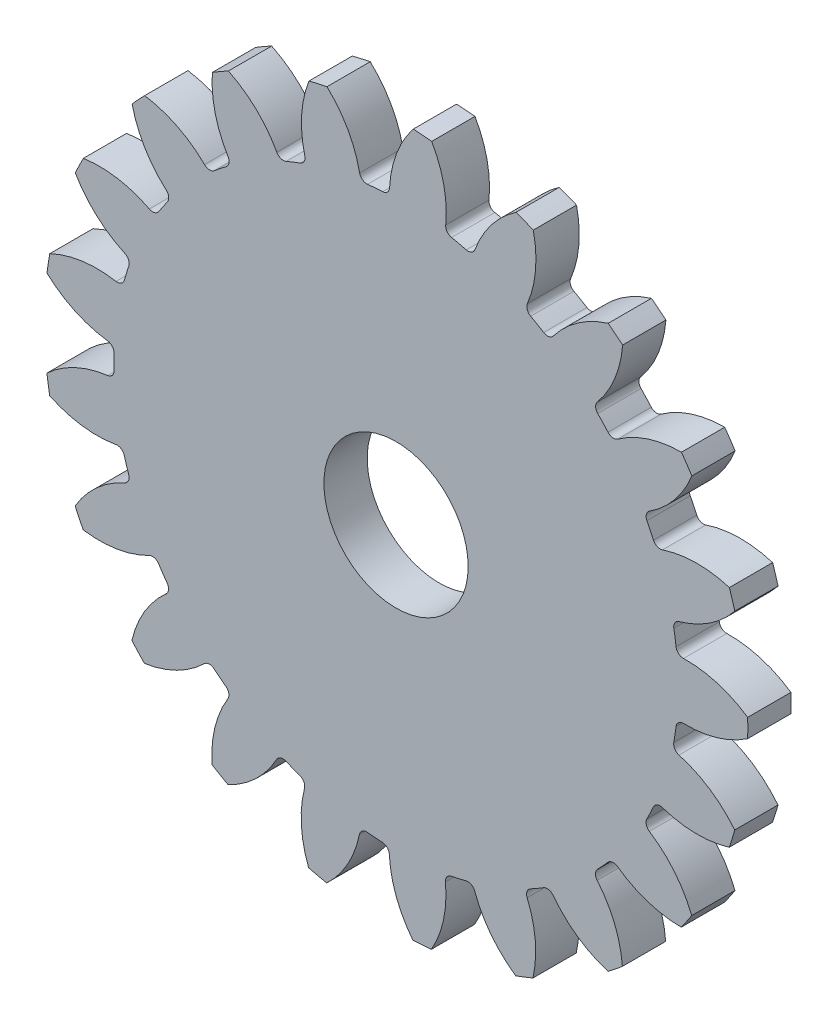
SolidWorks part; units mm, degrees
ref_plane "Alzado" through (0, 0, 0) normal (0, 0, 1) x (1, 0, 0)
ref_plane "Planta" through (0, 0, 0) normal (0, 1, 0) x (1, 0, 0)
ref_plane "Vista lateral" through (0, 0, 0) normal (1, 0, 0) x (0, 0, -1)
sketch "Croquis1" plane through (0, 0, 0) normal (0, 0, 1) x (1, 0, 0)
  circle A0 centre (0, 0) radius 24.384
  dimension "D1" = 48.768
extrude "Saliente-Extruir1" add sketch "Croquis1" along normal blind 3
sketch "Croquis2" plane through (0, 0, 3) normal (0, 0, 1) x (1, 0, 0)
  line L0 (0, 0) -> (0, 22.225) construction
  line L1 (0, 0) -> (8.7101, 23.9309) construction
  line L2 (0, 0) -> (-1.651, 22.1636) construction
  line L3 (0, 22.225) -> (7.143, 19.6252) construction
  arc A0 (1.1922, 24.3548) -> (-4.7875, 23.9094) centre (0, 0) ccw
  arc A2 (-0.4581, 19.5526) -> (-2.4439, 19.4047) centre (0, 0) ccw
  arc A3 (1.1922, 24.3548) -> (-0.4581, 19.5526) centre (7.143, 19.6252) ccw
  arc A4 (-4.7875, 23.9094) -> (-2.4439, 19.4047) centre (-9.9718, 18.3503) cw
  dimension "D2" = 39.116
  dimension "D3" = 20
  dimension "D4" = 1.651
extrude "Cortar-Extruir1" cut sketch "Croquis2" against normal through all
fillet "Redondeo1" radius 0.508 2 edges at (-0.4581, 19.5526, 1.5) (-2.4439, 19.4047, 1.5)
pattern_circular "MatrizC1" count 21 over 360 about axis through (0, 0, 0) along (0, 0, 1) of "Redondeo1", "Cortar-Extruir1"
sketch "Croquis3" plane through (0, 0, 3) normal (0, 0, 1) x (1, 0, 0)
  circle A0 centre (0, 0) radius 5
  dimension "D1" = 10
extrude "Cortar-Extruir2" cut sketch "Croquis3" against normal through all
